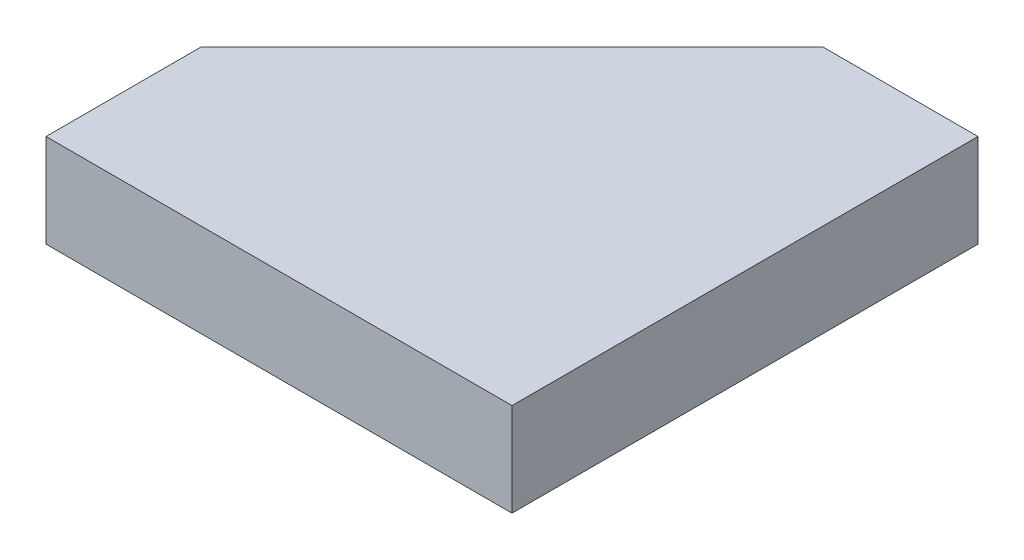
SolidWorks part; units mm, degrees
material "Maple"
ref_plane "Front Plane" through (0, 0, 0) normal (0, 0, 1) x (1, 0, 0)
ref_plane "Top Plane" through (0, 0, 0) normal (0, 1, 0) x (1, 0, 0)
ref_plane "Right Plane" through (0, 0, 0) normal (1, 0, 0) x (0, 0, -1)
sketch "Sketch1" plane through (0, 0, 0) normal (0, 1, 0) x (1, 0, 0)
  line L1 (-15, 15) -> (15, 15)
  line L2 (-15, 15) -> (-15, -15)
  line L3 (-15, -15) -> (15, -15)
  line L4 (15, 15) -> (15, -15)
  line L5 (-15, 15) -> (15, -15) construction
  line L6 (-15, -15) -> (15, 15) construction
  point P0 (0, 0)
  dimension "D1" = 30
  dimension "D2" = 30
extrude "Boss-Extrude1" add sketch "Sketch1" along normal blind 6
ref_plane "Plane1" through (0, 3, 0) normal (0, 1, 0) x (1, 0, 0)
chamfer "Chamfer1" distance 20 angle 45 1 edges at (-15, 3, -15)
